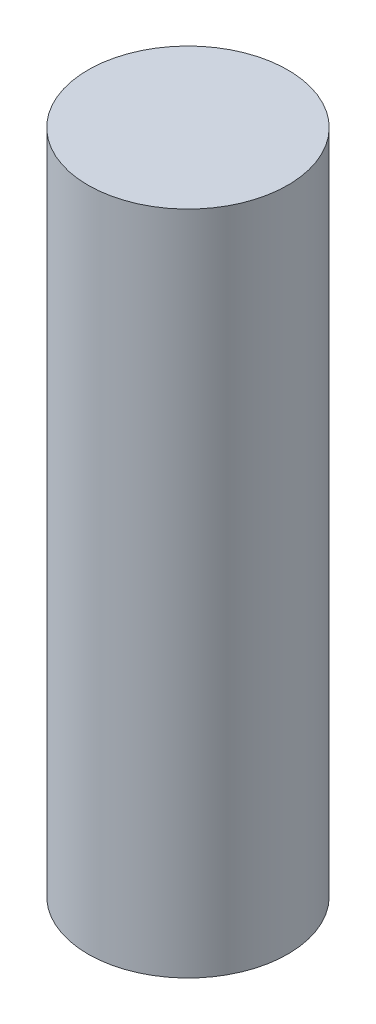
SolidWorks part; units mm, degrees
ref_plane "Front Plane" through (0, 0, 0) normal (0, 0, 1) x (1, 0, 0)
ref_plane "Top Plane" through (0, 0, 0) normal (0, 1, 0) x (1, 0, 0)
ref_plane "Right Plane" through (0, 0, 0) normal (1, 0, 0) x (0, 0, -1)
sketch "Sketch1" plane through (0, 0, 0) normal (0, 1, 0) x (1, 0, 0)
  circle A0 centre (0, 0) radius 9.525
  dimension "D1" = 19.05
extrude "Boss-Extrude1" add sketch "Sketch1" along normal blind 63.5
cosmetic thread "Cosmetic Thread1" parameters "D2"=16.0249
